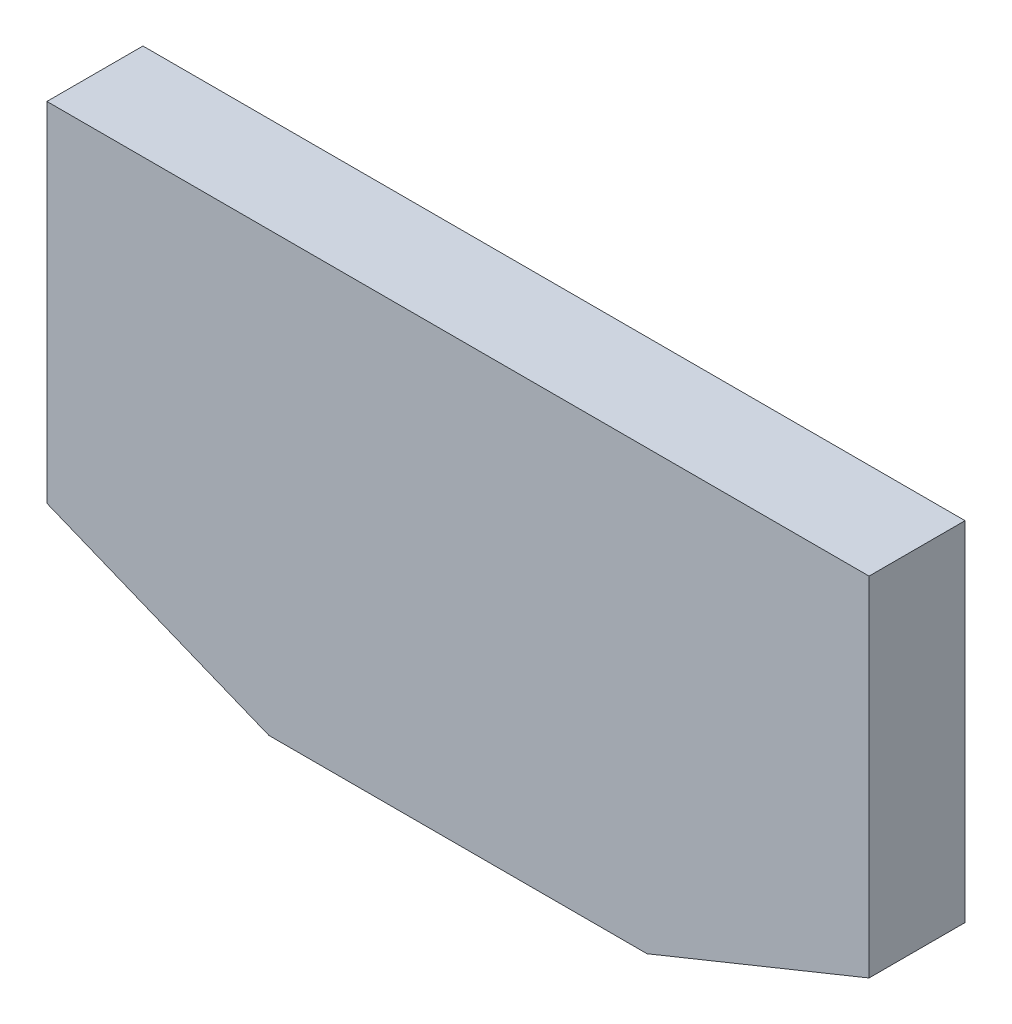
SolidWorks part; units mm, degrees
ref_plane "Front Plane" through (0, 0, 0) normal (0, 0, 1) x (1, 0, 0)
ref_plane "Top Plane" through (0, 0, 0) normal (0, 1, 0) x (1, 0, 0)
ref_plane "Right Plane" through (0, 0, 0) normal (1, 0, 0) x (0, 0, -1)
sketch "Sketch1" plane through (0, 0, 0) normal (0, 0, 1) x (1, 0, 0)
  line L0 (0, 75) -> (185, 0)
  line L1 (685, 75) -> (685, 365)
  line L2 (185, 0) -> (500, 0)
  line L3 (0, 365) -> (685, 365)
  line L5 (685, 75) -> (500, 0)
  line L6 (0, 75) -> (0, 365)
  point P0 (0, 0)
  dimension "D1" = 685
  dimension "D2" = 290
  dimension "D4" = 75
  dimension "D5" = 112.068
  dimension "D6" = 185
  dimension "D9" = 75
  dimension "D12" = 112.068
  dimension "D15" = 365
extrude "Extrude1" add sketch "Sketch1" along normal blind 7
sketch "Sketch2" plane through (0, 0, 0) normal (0, 0, -1) x (-1, 0, 0)
  line L1 (-685, 75) -> (0, 75)
  line L8 (0, 365) -> (-685, 365)
  line L9 (-685, 365) -> (-685, 75)
  line L10 (-685, 75) -> (-500, 0)
  line L11 (-500, 0) -> (-185, 0)
  line L12 (-185, 0) -> (0, 75)
  line L13 (0, 75) -> (0, 365)
  line L14 (0, 365) -> (-685, 365)
  line L15 (-685, 365) -> (-685, 75)
  line L19 (0, 75) -> (0, 365)
  dimension "D1" = 0
extrude "Extrude2" add sketch "Sketch2" along normal blind 73
